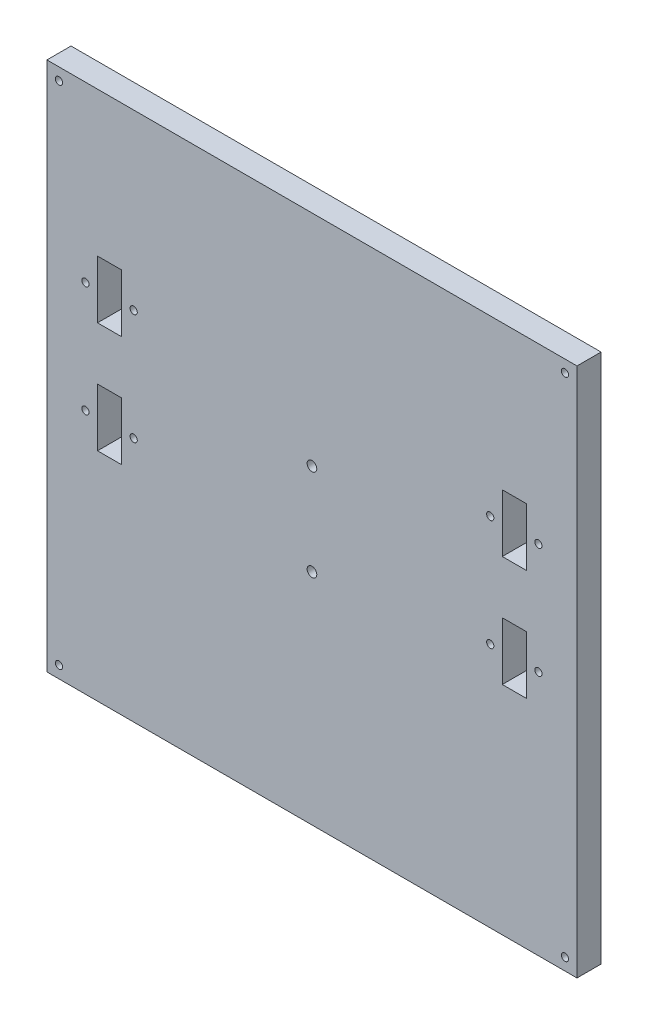
SolidWorks part; units mm, degrees
material "5052-H32"
ref_plane "Front Plane" through (0, 0, 0) normal (0, 0, 1) x (1, 0, 0)
ref_plane "Top Plane" through (0, 0, 0) normal (0, 1, 0) x (1, 0, 0)
ref_plane "Right Plane" through (0, 0, 0) normal (1, 0, 0) x (0, 0, -1)
sketch "Sketch2" plane through (0, 0, 0) normal (0, 0, 1) x (1, 0, 0)
  line L1 (112.5223, 130.8125) -> (332.5223, 130.8125)
  line L2 (112.5223, 130.8125) -> (112.5223, -89.1875)
  line L3 (112.5223, -89.1875) -> (332.5223, -89.1875)
  line L4 (332.5223, 130.8125) -> (332.5223, -89.1875)
  dimension "D1" = 220
  dimension "D2" = 220
extrude "Boss-Extrude2" add sketch "Sketch2" along normal blind 10 separate body
sketch "Sketch3" plane through (0, 0, 10) normal (0, 0, 1) x (1, 0, 0)
  line L0 (112.5223, 130.8125) -> (112.5223, -89.1875) construction
  line L5 (332.5223, 130.8125) -> (112.5223, 130.8125) construction
  line L6 (112.5223, -89.1875) -> (332.5223, -89.1875) construction
  line L7 (332.5223, -89.1875) -> (332.5223, 130.8125) construction
  circle A0 centre (117.5223, 125.8125) radius 1.5
  circle A1 centre (117.5223, -84.1875) radius 1.5
  circle A2 centre (327.5223, -84.1875) radius 1.5
  circle A3 centre (327.5223, 125.8125) radius 1.5
  dimension "D1" = 5
  dimension "D3" = 5
  dimension "D5" = 5
  dimension "D7" = 5
  dimension "D2" = 5
  dimension "D4" = 5
  dimension "D6" = 5
  dimension "D8" = 5
extrude "Cut-Extrude2" cut sketch "Sketch3" against normal blind 10
sketch "Sketch4" plane through (0, 0, 10) normal (0, 0, 1) x (1, 0, 0)
  line L1 (133.5223, 70.8125) -> (143.5223, 70.8125)
  line L2 (133.5223, 70.8125) -> (133.5223, 46.8125)
  line L3 (133.5223, 46.8125) -> (143.5223, 46.8125)
  line L4 (143.5223, 70.8125) -> (143.5223, 46.8125)
  line L5 (112.5223, 130.8125) -> (112.5223, -89.1875) construction
  line L6 (332.5223, 130.8125) -> (112.5223, 130.8125) construction
  line L7 (332.5223, -89.1875) -> (332.5223, 130.8125) construction
  line L8 (133.5223, 24.8125) -> (143.5223, 24.8125)
  line L9 (133.5223, 24.8125) -> (133.5223, 0.8125)
  line L10 (133.5223, 0.8125) -> (143.5223, 0.8125)
  line L11 (143.5223, 24.8125) -> (143.5223, 0.8125)
  line L12 (301.5223, 70.8125) -> (311.5223, 70.8125)
  line L13 (301.5223, 70.8125) -> (301.5223, 46.8125)
  line L14 (301.5223, 46.8125) -> (311.5223, 46.8125)
  line L15 (311.5223, 70.8125) -> (311.5223, 46.8125)
  line L16 (301.5223, 24.8125) -> (311.5223, 24.8125)
  line L17 (301.5223, 24.8125) -> (301.5223, 0.8125)
  line L18 (301.5223, 0.8125) -> (311.5223, 0.8125)
  line L19 (311.5223, 24.8125) -> (311.5223, 0.8125)
  line L20 (112.5223, -89.1875) -> (332.5223, -89.1875) construction
  circle A0 centre (128.5223, 58.8125) radius 1.5
  circle A1 centre (148.5223, 58.8125) radius 1.5
  circle A2 centre (128.5223, 12.8125) radius 1.5
  circle A3 centre (148.5223, 12.8125) radius 1.5
  circle A4 centre (296.5223, 12.8125) radius 1.5
  circle A5 centre (316.5223, 12.8125) radius 1.5
  circle A6 centre (296.5223, 58.8125) radius 1.5
  circle A7 centre (316.5223, 58.8125) radius 1.5
  dimension "D3" = 5
  dimension "D5" = 12
  dimension "D15" = 12
  dimension "D16" = 12
  dimension "D17" = 12
  dimension "D18" = 12
  dimension "D19" = 12
  dimension "D20" = 12
  dimension "D21" = 5
  dimension "D22" = 5
  dimension "D23" = 5
  dimension "D24" = 5
  dimension "D25" = 5
  dimension "D1" = 24
  dimension "D2" = 10
  dimension "D4" = 5
  dimension "D6" = 12
  dimension "D7" = 21
  dimension "D8" = 60
  dimension "D9" = 10
  dimension "D10" = 10
  dimension "D11" = 10
  dimension "D12" = 24
  dimension "D13" = 24
  dimension "D14" = 24
  dimension "D26" = 5
  dimension "D27" = 60
  dimension "D28" = 21
  dimension "D29" = 21
  dimension "D30" = 21
  dimension "D31" = 90
  dimension "D32" = 90
extrude "Cut-Extrude3" cut sketch "Sketch4" against normal blind 10
sketch "Sketch6" plane through (0, 0, 10) normal (0, 0, 1) x (1, 0, 0)
  line L0 (112.5223, 130.8125) -> (112.5223, -89.1875) construction
  line L1 (332.5223, 130.8125) -> (112.5223, 130.8125) construction
  circle A0 centre (222.5223, 39.8125) radius 2
  circle A1 centre (222.5223, 1.8125) radius 2
  dimension "D1" = 110
  dimension "D2" = 110
  dimension "D3" = 38
  dimension "D4" = 91
extrude "Cut-Extrude4" cut sketch "Sketch6" against normal blind 10
